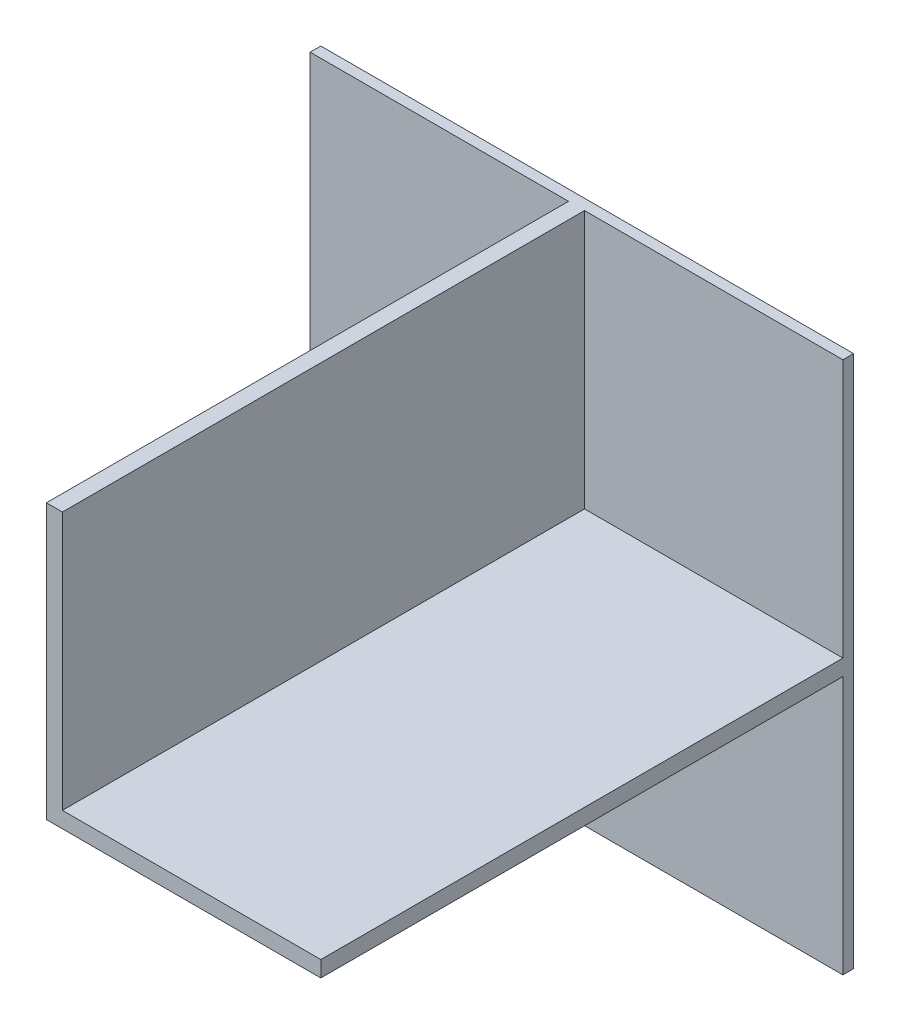
SolidWorks part; units mm, degrees
ref_plane "Płaszczyzna przednia" through (0, 0, 0) normal (0, 0, 1) x (1, 0, 0)
ref_plane "Płaszczyzna górna" through (0, 0, 0) normal (0, 1, 0) x (1, 0, 0)
ref_plane "Płaszczyzna prawa" through (0, 0, 0) normal (1, 0, 0) x (0, 0, -1)
sketch "Szkic1" plane through (0, 0, 0) normal (0, 0, 1) x (1, 0, 0)
  line L0 (0, 0) -> (100, 0)
  line L1 (0, 0) -> (-100, 0)
  line L2 (0, 0) -> (0, 100)
  line L3 (0, 0) -> (0, -100)
  line L4 (0, 100) -> (100, 100)
  line L5 (100, 100) -> (100, 0)
  line L6 (100, -100) -> (0, -100)
  line L7 (100, 0) -> (100, -100)
  line L8 (0, 100) -> (-100, 100)
  line L9 (-100, 100) -> (-100, 0)
  line L10 (-100, -100) -> (-100, 0)
  line L11 (0, -100) -> (-100, -100)
  dimension "D1" = 100
  dimension "D2" = 100
  dimension "D3" = 100
  dimension "D4" = 100
  dimension "D5" = 100
  dimension "D6" = 100
  dimension "D7" = 100
  dimension "D8" = 100
  dimension "D9" = 100
  dimension "D10" = 100
  dimension "D11" = 100
extrude "Dodanie-wyciągnięcie1" add sketch "Szkic1" along normal blind 4 contours L8 L9 L1 L2 | L5 L4 L2 L0 | L7 L0 L3 L6 | L11 L3 L1 L10
sketch "Szkic2" plane through (0, 0, 4) normal (0, 0, 1) x (1, 0, 0)
  line L1 (100, 100) -> (-100, 100) construction
  line L2 (100, -100) -> (-100, -100) construction
  line L9 (-2, -100) -> (2, -100)
  line L14 (100, 100) -> (100, -100) construction
  line L20 (0, 0) -> (0, 3)
  line L21 (0, 0) -> (-3, 0)
  line L22 (0, 0) -> (3, 0)
  line L23 (-3, 0) -> (-3, 100)
  line L24 (3, 0) -> (3, 100)
  line L25 (0, -3) -> (100, -3)
  line L26 (3, 3) -> (100, 3)
  line L27 (-3, -3) -> (-3, 0)
  line L28 (0, -3) -> (-3, -3)
  line L29 (100, 3) -> (100, -3)
  line L30 (-3, 100) -> (3, 100)
  dimension "D2" = 3
  dimension "D7" = 3
  dimension "D8" = 4
  dimension "D11" = 3
  dimension "D12" = 3
extrude "Dodanie-wyciągnięcie3" add sketch "Szkic2" along normal blind 196
